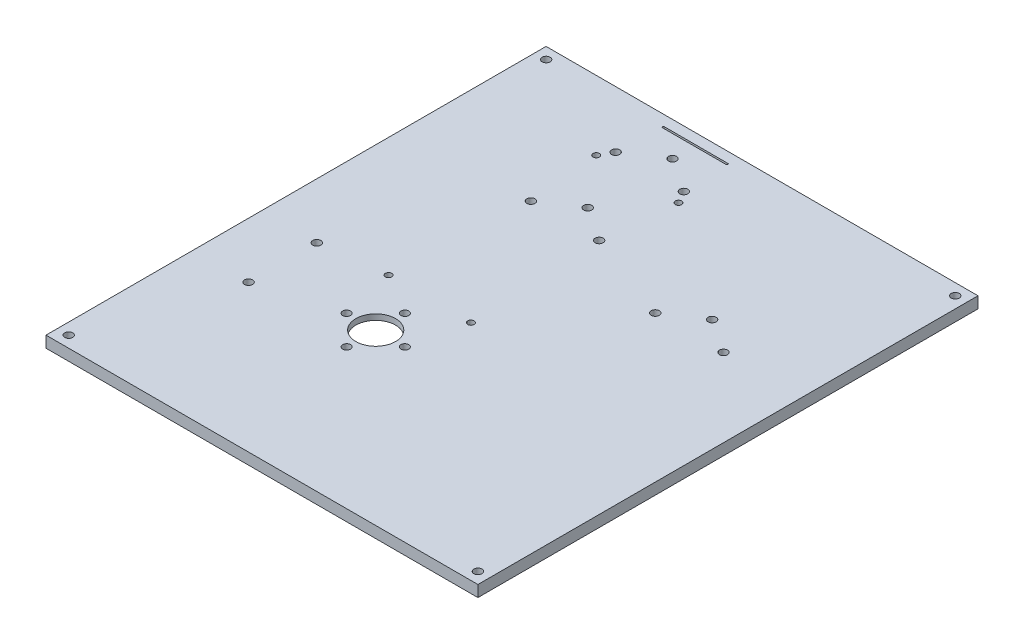
SolidWorks part; units mm, degrees
material "6061-T6 (SS)"
ref_plane "Front Plane" through (0, 0, 0) normal (0, 0, 1) x (1, 0, 0)
ref_plane "Top Plane" through (0, 0, 0) normal (0, 1, 0) x (1, 0, 0)
ref_plane "Right Plane" through (0, 0, 0) normal (1, 0, 0) x (0, 0, -1)
sketch "Sketch1" plane through (0, 0, 0) normal (0, 1, 0) x (1, 0, 0)
  line L1 (-50.8, 50.8) -> (50.8, 50.8)
  line L2 (-50.8, 50.8) -> (-50.8, -50.8)
  line L3 (-50.8, -50.8) -> (50.8, -50.8)
  line L4 (50.8, 50.8) -> (50.8, -50.8)
  line L5 (-50.8, 50.8) -> (50.8, -50.8) construction
  line L6 (-50.8, -50.8) -> (50.8, 50.8) construction
  point P0 (0, 0)
  dimension "D1" = 101.6
  dimension "D2" = 101.6
extrude "Boss-Extrude1" add sketch "Sketch1" along normal blind 3.175
sketch "Sketch3" plane through (0, 3.175, 0) normal (0, 1, 0) x (1, 0, 0)
  line L0 (50.8, 50.8) -> (-50.8, 50.8) construction
  line L1 (50.8, 50.8) -> (101.6, 50.8)
  line L2 (50.8, 50.8) -> (50.8, -50.8)
  line L3 (50.8, -50.8) -> (101.6, -50.8)
  line L4 (101.6, 50.8) -> (101.6, -50.8)
  line L5 (50.8, -50.8) -> (50.8, 50.8) construction
  dimension "D1" = 50.8
extrude "Boss-Extrude2" add sketch "Sketch3" against normal up to surface (3.175 mm away) up to face at (0, 0, 0)
sketch "Sketch6" plane through (0, 3.175, 0) normal (0, 1, 0) x (1, 0, 0)
  line L0 (101.6, -50.8) -> (101.6, 50.8) construction
  line L1 (-50.8, 50.8) -> (101.6, 50.8)
  line L2 (-50.8, 50.8) -> (-50.8, 88.9)
  line L3 (-50.8, 88.9) -> (101.6, 88.9)
  line L4 (101.6, 50.8) -> (101.6, 88.9)
  line L5 (101.6, 50.8) -> (-50.8, 50.8) construction
  dimension "D1" = 38.1
extrude "Boss-Extrude4" add sketch "Sketch6" against normal up to surface (3.175 mm away) up to face at (25.4, 0, 0)
sketch "Sketch9" plane through (0, 3.175, 0) normal (0, 1, 0) x (1, 0, 0)
  line L0 (-50.8, -50.8) -> (101.6, -50.8) construction
  line L1 (-50.8, 88.9) -> (-57.15, 88.9)
  line L2 (-50.8, 88.9) -> (-50.8, -50.8)
  line L3 (-50.8, -50.8) -> (-57.15, -50.8)
  line L4 (-57.15, 88.9) -> (-57.15, -50.8)
  line L5 (-50.8, 88.9) -> (-50.8, -50.8) construction
  dimension "D1" = 6.35
extrude "Boss-Extrude5" add sketch "Sketch9" against normal up to surface (3.175 mm away) up to face at (25.4, 0, -19.05)
sketch "Sketch7" plane through (0, 3.175, 0) normal (0, 1, 0) x (1, 0, 0)
  line L0 (-57.15, -50.8) -> (101.6, -50.8) construction
  line L1 (-57.15, 88.9) -> (63.5, 88.9)
  line L2 (-57.15, 88.9) -> (-57.15, -50.8)
  line L3 (-57.15, -50.8) -> (63.5, -50.8)
  line L4 (63.5, 88.9) -> (63.5, -50.8)
  dimension "D1" = 120.65
extrude "Cut-Extrude3" cut sketch "Sketch7" against normal through all flip side to cut
hole_wizard "#4-40 Tapped Hole2" positions "Sketch13" profile "Sketch14" tap size "#4-40" standard "ANSI Inch" end condition through all
sketch "Sketch13" plane through (0, 3.175, 0) normal (0, 1, 0) x (1, 0, 0)
  point P17 (32.1308, 46.001)
  point P31 (-2.7942, 49.351)
  point P33 (-12.3192, 55.701)
  point P35 (-21.8442, 49.351)
  point P50 (22.6058, 39.651)
  point P52 (41.6558, 39.651)
  point P61 (-41.6626, 9.3559)
  point P63 (-41.6626, -9.6941)
  point P72 (-2.7942, 73.025)
  point P74 (-12.3192, 79.375)
  point P76 (-21.8442, 73.025)
  point P88 (60.325, -47.625)
  point P90 (-53.975, -47.625)
  point P92 (60.325, 85.725)
  point P94 (-53.975, 85.725)
sketch "Sketch14" plane through (32.1308, 3.175, -46.001) normal (1, 0, 0) x (0, 0, 1)
  line L0 (0, 0) -> (0, 3.175)
  line L1 (0, 3.175) -> (1.1303, 3.175)
  line L2 (1.1303, 3.175) -> (1.1303, 0)
  line L3 (1.1303, 0) -> (0, 0)
  line L4 (0, -6.35) -> (0, 107.95) construction
  dimension "Thru Tap Drill Dia." = 2.2606
  dimension "Thru Tap Drill Depth" = 3.175
cosmetic thread "Hole Thread8" parameters "D2"=2.8448
cosmetic thread "Hole Thread13" [suppressed] parameters "D2"=2.8448
cosmetic thread "Hole Thread14" [suppressed] parameters "D2"=2.8448
cosmetic thread "Hole Thread15" [suppressed] parameters "D2"=2.8448
cosmetic thread "Hole Thread16" [suppressed] parameters "D2"=2.8448
cosmetic thread "Hole Thread20" [suppressed] parameters "D2"=2.8448
cosmetic thread "Hole Thread22" [suppressed] parameters "D2"=2.8448
cosmetic thread "Hole Thread24" [suppressed] parameters "D2"=2.8448
cosmetic thread "Hole Thread25" [suppressed] parameters "D2"=2.8448
cosmetic thread "Hole Thread26" [suppressed] parameters "D2"=2.8448
cosmetic thread "Hole Thread27" [suppressed] parameters "D2"=2.8448
cosmetic thread "Hole Thread28" [suppressed] parameters "D2"=2.8448
cosmetic thread "Hole Thread29" [suppressed] parameters "D2"=2.8448
cosmetic thread "Hole Thread30" [suppressed] parameters "D2"=2.8448
cosmetic thread "Hole Thread31" [suppressed] parameters "D2"=2.8448
sketch "Sketch15" plane through (0, 0, 0) normal (0, -1, 0) x (1, 0, 0)
  line L8 (-55.5625, -87.3125) -> (61.9125, -87.3125)
  line L9 (61.9125, -87.3125) -> (61.9125, 49.2125)
  line L10 (-55.5625, 49.2125) -> (-55.5625, -87.3125)
  line L11 (61.9125, 49.2125) -> (-55.5625, 49.2125)
  line L12 (-52.2001, -87.3125) -> (58.5501, -87.3125)
  line L13 (61.9125, -83.9501) -> (61.9125, 45.8501)
  line L14 (-55.5625, 45.8501) -> (-55.5625, -83.9501)
  line L15 (58.5501, 49.2125) -> (-52.2001, 49.2125)
  circle A1 centre (32.1308, -46.001) radius 2.3812
  circle A2 centre (-2.7942, -49.351) radius 2.3812
  circle A3 centre (-12.3192, -55.701) radius 2.3812
  circle A4 centre (-21.8442, -49.351) radius 2.3812
  circle A8 centre (41.6558, -39.651) radius 2.3812
  circle A9 centre (22.6058, -39.651) radius 2.3812
  circle A10 centre (-41.6626, 9.6941) radius 2.3812
  circle A11 centre (-41.6626, -9.3559) radius 2.3812
  circle A12 centre (-2.7942, -73.025) radius 2.3812
  circle A13 centre (-12.3192, -79.375) radius 2.3812
  circle A14 centre (-21.8442, -73.025) radius 2.3812
  arc A15 (-55.5625, 45.8501) -> (-52.2001, 49.2125) centre (-53.975, 47.625) ccw
  arc A16 (58.5501, 49.2125) -> (61.9125, 45.8501) centre (60.325, 47.625) ccw
  arc A17 (61.9125, -83.9501) -> (58.5501, -87.3125) centre (60.325, -85.725) ccw
  arc A18 (-52.2001, -87.3125) -> (-55.5625, -83.9501) centre (-53.975, -85.725) ccw
  dimension "D1" = 4.7625
  dimension "D2" = 2.3812
  dimension "D3" = 1.5875
extrude "Cut-Extrude5" cut sketch "Sketch15" against normal blind 1.5875
fillet "Fillet1" radius 3.429 8 edges at (58.5501, 0.7937, 49.2125) (61.9125, 0.7937, 45.8501) (-55.5625, 0.7937, 45.8501) (-52.2001, 0.7937, 49.2125) (-55.5625, 0.7937, -83.9501) (-52.2001, 0.7937, -87.3125) (58.5501, 0.7937, -87.3125) (61.9125, 0.7937, -83.9501)
hole_wizard "#2-56 Tapped Hole" positions "Sketch16" profile "Sketch17" tap size "#2-56" standard "ANSI Inch" end condition through all
sketch "Sketch16" plane through (0, 3.175, 0) normal (0, 1, 0) x (1, 0, 0)
  point P0 (-0.8192, 11.5576)
  point P2 (-23.8192, 11.5576)
  point P4 (-0.8192, 69.5576)
  point P6 (-23.8192, 69.5576)
sketch "Sketch17" plane through (-0.8192, 3.175, -11.5576) normal (1, 0, 0) x (0, 0, 1)
  line L0 (0, 0) -> (0, 3.175)
  line L1 (0, 3.175) -> (0.889, 3.175)
  line L2 (0.889, 3.175) -> (0.889, 0)
  line L3 (0.889, 0) -> (0, 0)
  line L4 (0, -6.35) -> (0, 107.95) construction
  dimension "Thread Major Dia." = 1.778
  dimension "Thru Tap Drill Depth" = 3.175
sketch "Sketch19" plane through (0, 1.5875, 0) normal (0, 1, 0) x (1, 0, 0)
  circle A0 centre (-23.8192, 69.5576) radius 0.889 construction
  circle A1 centre (-0.8192, 69.5576) radius 0.889 construction
  circle A2 centre (-23.8192, 11.5576) radius 0.889 construction
  circle A3 centre (-0.8192, 11.5576) radius 0.889 construction
  circle A4 centre (-23.8192, 69.5576) radius 0.889
  circle A5 centre (-0.8192, 69.5576) radius 0.889
  circle A6 centre (-23.8192, 11.5576) radius 0.889
  circle A7 centre (-0.8192, 11.5576) radius 0.889
  circle A8 centre (-23.8192, 69.5576) radius 2.4765
  circle A9 centre (-0.8192, 69.5576) radius 2.4765
  circle A10 centre (-23.8192, 11.5576) radius 2.4765
  circle A11 centre (-0.8192, 11.5576) radius 2.4765
  dimension "D1" = 1.5875
extrude "Boss-Extrude6" add sketch "Sketch19" against normal up to surface (1.5875 mm away) up to face at (32.1308, 0, -44.8707)
extrude "Cut-Extrude7" cut sketch "Sketch21" against normal through all
sketch "Sketch21" plane through (0, 3.175, 0) normal (0, 1, 0) x (1, 0, 0)
  circle A0 centre (-12.3192, -3.524) radius 5.55
sketch "Sketch22" plane through (0, 1.5875, 0) normal (0, -1, 0) x (1, 0, 0)
  line L0 (-21.2092, -85.725) -> (-3.4292, -85.725) construction
  line L1 (-21.2092, -85.471) -> (-3.4292, -85.471)
  line L2 (-21.2092, -85.979) -> (-3.4292, -85.979)
  line L3 (-12.3192, -85.725) -> (-12.3192, -79.375) construction
  line L4 (-57.15, -88.9) -> (63.5, -88.9) construction
  arc A0 (-21.2092, -85.471) -> (-21.2092, -85.979) centre (-21.2092, -85.725) ccw
  arc A1 (-3.4292, -85.979) -> (-3.4292, -85.471) centre (-3.4292, -85.725) ccw
  point P2 (-12.3192, -85.725)
  dimension "D1" = 0.508
  dimension "D2" = 17.78
  dimension "D3" = 3.175
extrude "Cut-Extrude8" cut sketch "Sketch22" against normal through all
hole_wizard "M2 Clearance Hole1" positions "Sketch23" profile "Sketch24" hole size "M2" standard "ANSI Metric" end condition through all
sketch "Sketch23" plane through (0, 3.175, 0) normal (0, 1, 0) x (1, 0, 0)
  point P0 (-20.4509, -3.524)
  point P2 (-12.3192, -11.6558)
  point P4 (-4.1875, -3.524)
  point P6 (-12.3192, 4.6077)
sketch "Sketch24" plane through (-20.4509, 3.175, 3.524) normal (1, 0, 0) x (0, 0, 1)
  line L0 (0, 0) -> (0, 3.175)
  line L1 (0, 3.175) -> (1.1, 3.175)
  line L2 (1.1, 3.175) -> (1.1, 0)
  line L3 (1.1, 0) -> (0, 0)
  line L4 (0, -6.35) -> (0, 107.95) construction
  dimension "Thru Hole Dia." = 2.2
  dimension "Thru Hole Depth" = 3.175
